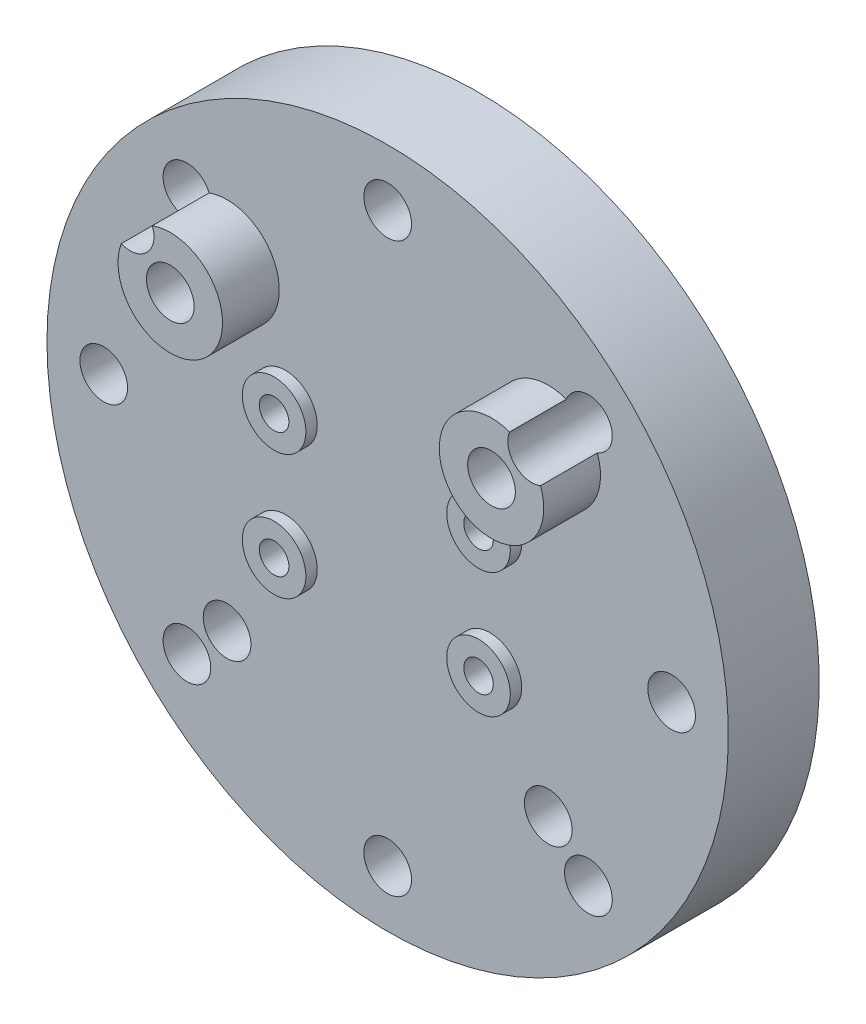
SolidWorks part; units mm, degrees
material "ABS"
ref_plane "Plan de face" through (0, 0, 0) normal (0, 0, 1) x (1, 0, 0)
ref_plane "Plan de dessus" through (0, 0, 0) normal (0, 1, 0) x (1, 0, 0)
ref_plane "Plan de droite" through (0, 0, 0) normal (1, 0, 0) x (0, 0, -1)
sketch "Esquisse1" plane through (0, 0, 0) normal (0, 0, 1) x (1, 0, 0)
  line L0 (-14.1421, 14.1421) -> (14.1421, 14.1421) construction
  line L1 (9, 5.5) -> (-9, 5.5) construction
  line L2 (9, 5.5) -> (9, -5.5) construction
  line L3 (9, -5.5) -> (-9, -5.5) construction
  line L4 (-9, 5.5) -> (-9, -5.5) construction
  line L5 (9, 5.5) -> (-9, -5.5) construction
  line L6 (9, -5.5) -> (-9, 5.5) construction
  line L7 (14.1421, 14.1421) -> (14.1421, -14.1421) construction
  line L8 (14.1421, -14.1421) -> (-14.1421, -14.1421) construction
  line L9 (-14.1421, -14.1421) -> (-14.1421, 14.1421) construction
  circle A0 centre (0, 0) radius 20 construction
  circle A1 centre (-14.1421, 14.1421) radius 2.1
  circle A2 centre (14.1421, 14.1421) radius 2.1
  circle A3 centre (14.1421, -14.1421) radius 2.1 construction
  circle A4 centre (-14.1421, -14.1421) radius 2.1 construction
  circle A5 centre (0, 0) radius 25
  circle A6 centre (-9, 5.5) radius 1.3
  circle A7 centre (-9, -5.5) radius 1.3
  circle A8 centre (9, 5.5) radius 1.3
  circle A9 centre (9, -5.5) radius 1.3
  point P0 (0, 0)
  dimension "D3" = 40
  dimension "D4" = 4.2
  dimension "D5" = 4.2
  dimension "D6" = 4.2
  dimension "D7" = 4.2
  dimension "D8" = 50
  dimension "D9" = 2.6
  dimension "D10" = 2.6
  dimension "D11" = 2.6
  dimension "D12" = 2.6
  dimension "D1" = 18
  dimension "D2" = 11
extrude "Boss.-Extru.1" add sketch "Esquisse1" along normal blind 2
sketch "Esquisse2" plane through (0, 0, 2) normal (0, 0, 1) x (1, 0, 0)
  line L0 (0, -14) -> (0, 0) construction
  line L1 (11, -19) -> (-11, -19)
  line L2 (11, -19) -> (11, -9)
  line L3 (11, -9) -> (-11, -9)
  line L4 (-11, -19) -> (-11, -9)
  line L5 (11, -19) -> (-11, -9) construction
  line L6 (11, -9) -> (-11, -19) construction
  point P0 (0, -14)
  dimension "D1" = 9
  dimension "D2" = 22
  dimension "D3" = 10
extrude "Enlèv. mat.-Extru.1" cut sketch "Esquisse2" against normal blind 2
sketch "Esquisse3" plane through (0, 0, 2) normal (0, 0, 1) x (1, 0, 0)
  circle A2 centre (-9, -5.5) radius 1.3 construction
  circle A3 centre (9, -5.5) radius 1.3 construction
  circle A4 centre (9, 5.5) radius 1.3 construction
  circle A5 centre (-14.1421, 14.1421) radius 2.1 construction
  circle A6 centre (-9, 5.5) radius 1.3 construction
  circle A7 centre (14.1421, -14.1421) radius 2.1
  circle A8 centre (-14.1421, -14.1421) radius 2.1
  circle A9 centre (-9, -5.5) radius 1.3
  circle A10 centre (9, -5.5) radius 1.3
  circle A11 centre (9, 5.5) radius 1.3
  circle A12 centre (-14.1421, 14.1421) radius 2.1
  circle A13 centre (-9, 5.5) radius 1.3
  circle A14 centre (-9, -5.5) radius 2.8
  circle A15 centre (9, -5.5) radius 2.8
  circle A16 centre (9, 5.5) radius 2.8
  circle A17 centre (-9, 5.5) radius 2.8
  circle A18 centre (-14.1421, 14.1421) radius 4.6
  circle A19 centre (14.1421, -14.1421) radius 3.6
  circle A20 centre (-14.1421, -14.1421) radius 3.6
  circle A21 centre (14.1421, 14.1421) radius 2.1 construction
  circle A22 centre (14.1421, 14.1421) radius 2.1
  circle A23 centre (14.1421, 14.1421) radius 4.6
  dimension "D1" = 1.5
  dimension "D2" = 2.5
  dimension "D3" = 1.5
  dimension "D4" = 2.5
extrude "Boss.-Extru.2" add sketch "Esquisse3" along normal blind 1
sketch "Esquisse4" plane through (0, 0, 0) normal (0, 0, -1) x (-1, 0, 0)
  line L0 (-14.1421, 18.7421) -> (14.1421, 18.7421)
  line L1 (-18.7421, 14.1421) -> (-18.7421, -9)
  line L2 (18.7421, 14.1421) -> (18.7421, -9)
  line L4 (18.7421, -9) -> (-18.7421, -9)
  circle A0 centre (-14.1421, 14.1421) radius 4.6 construction
  circle A1 centre (14.1421, 14.1421) radius 4.6 construction
  circle A4 centre (-14.1421, 14.1421) radius 4.6 construction
  arc A5 (-14.1421, 18.7421) -> (-18.7421, 14.1421) centre (-14.1421, 14.1421) ccw
  circle A6 centre (14.1421, 14.1421) radius 4.6 construction
  arc A7 (18.7421, 14.1421) -> (14.1421, 18.7421) centre (14.1421, 14.1421) ccw
  dimension "D1" = 9
extrude "Enlèv. mat.-Extru.2" cut sketch "Esquisse4" against normal through all flip side to cut
fillet "Congé1" radius 2 2 edges at (18.7421, -9, 1) (-18.7421, -9, 1)
sketch "Esquisse5" plane through (0, 0, 3) normal (0, 0, 1) x (1, 0, 0)
  circle A2 centre (14.1421, 14.1421) radius 4.6 construction
  circle A3 centre (-14.1421, 14.1421) radius 4.6 construction
  circle A4 centre (-14.1421, -14.1421) radius 3.6 construction
  circle A5 centre (14.1421, -14.1421) radius 3.6 construction
  circle A6 centre (14.1421, 14.1421) radius 4.6
  circle A7 centre (-14.1421, 14.1421) radius 4.6
  circle A9 centre (14.1421, 14.1421) radius 2.1 construction
  circle A11 centre (-14.1421, 14.1421) radius 2.1 construction
  circle A12 centre (14.1421, -14.1421) radius 2.1 construction
  circle A13 centre (14.1421, 14.1421) radius 2.1
  circle A14 centre (-14.1421, -14.1421) radius 2.1 construction
  circle A15 centre (-14.1421, 14.1421) radius 2.1
extrude "Boss.-Extru.3" add sketch "Esquisse5" along normal blind 4
sketch "Esquisse6" plane through (0, 0, 0) normal (0, 0, -1) x (-1, 0, 0)
  circle A0 centre (0, 0) radius 30
  circle A1 centre (14.1421, 14.1421) radius 2.1 construction
  circle A2 centre (9, 5.5) radius 1.3 construction
  circle A3 centre (9, -5.5) radius 1.3 construction
  circle A4 centre (-9, -5.5) radius 1.3 construction
  circle A5 centre (-9, 5.5) radius 1.3 construction
  circle A6 centre (-14.1421, 14.1421) radius 2.1 construction
  circle A7 centre (14.1421, 14.1421) radius 2.1
  circle A8 centre (9, 5.5) radius 1.3
  circle A9 centre (9, -5.5) radius 1.3
  circle A10 centre (-9, -5.5) radius 1.3
  circle A11 centre (-9, 5.5) radius 1.3
  circle A12 centre (-14.1421, 14.1421) radius 2.1
  dimension "D1" = 60
extrude "Boss.-Extru.4" add sketch "Esquisse6" against normal blind 2 and the other way blind 6
sketch "Esquisse7" plane through (0, 0, -6) normal (0, 0, -1) x (-1, 0, 0)
  line L0 (-14.1421, 14.1421) -> (-14.1421, -14.1421) construction
  line L1 (14.1421, 14.1421) -> (14.1421, -14.1421) construction
  line L2 (-14.1421, -14.1421) -> (14.1421, -14.1421) construction
  circle A0 centre (0, 0) radius 20 construction
  circle A1 centre (-14.1421, -14.1421) radius 2.1
  circle A2 centre (14.1421, -14.1421) radius 2.1
  circle A3 centre (0, 0) radius 25 construction
  circle A4 centre (0, 25) radius 2.1
  circle A5 centre (17.6777, 17.6777) radius 2.1
  circle A6 centre (25, 0) radius 2.1
  circle A7 centre (17.6777, -17.6777) radius 2.1
  circle A8 centre (0, -25) radius 2.1
  circle A9 centre (-17.6777, -17.6777) radius 2.1
  circle A10 centre (-25, 0) radius 2.1
  circle A11 centre (-17.6777, 17.6777) radius 2.1
  point P30 (0, 0)
  dimension "D1" = 4.2
  dimension "D2" = 4.2
  dimension "D3" = 50
  dimension "D4" = 4.2
  dimension "D5" = 8
extrude "Enlèv. mat.-Extru.3" cut sketch "Esquisse7" against normal through all
sketch "Esquisse8" plane through (0, 0, -6) normal (0, 0, -1) x (-1, 0, 0)
  circle A0 centre (-14.1421, -14.1421) radius 2.1 construction
  circle A1 centre (14.1421, -14.1421) radius 2.1 construction
  circle A2 centre (14.1421, 14.1421) radius 2.1 construction
  circle A3 centre (-14.1421, 14.1421) radius 2.1 construction
  circle A4 centre (-14.1421, -14.1421) radius 2.1
  circle A5 centre (14.1421, -14.1421) radius 2.1
  circle A6 centre (14.1421, 14.1421) radius 2.1
  circle A7 centre (-14.1421, 14.1421) radius 2.1
  circle A8 centre (-14.1421, -14.1421) radius 3.6
  circle A9 centre (14.1421, -14.1421) radius 3.6
  circle A10 centre (14.1421, 14.1421) radius 3.6
  circle A11 centre (-14.1421, 14.1421) radius 3.6
  dimension "D1" = 1.5
extrude "Enlèv. mat.-Extru.4" cut sketch "Esquisse8" against normal blind 3
